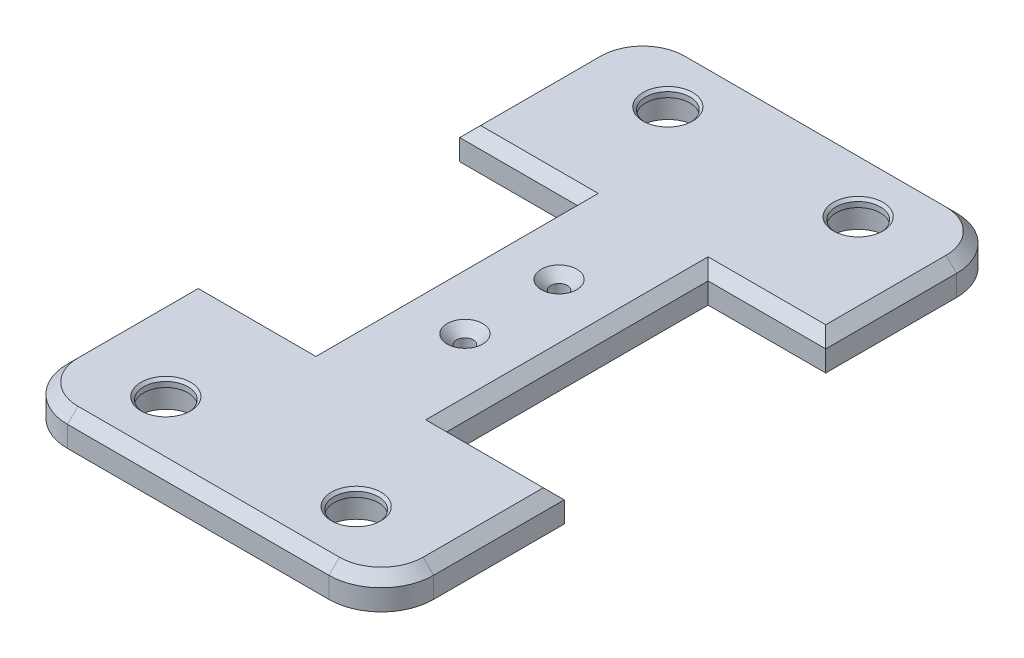
SolidWorks part; units mm, degrees
ref_plane "Plan de face" through (0, 0, 0) normal (0, 0, 1) x (1, 0, 0)
ref_plane "Plan de dessus" through (0, 0, 0) normal (0, 1, 0) x (1, 0, 0)
ref_plane "Plan de droite" through (0, 0, 0) normal (1, 0, 0) x (0, 0, -1)
sketch "Esquisse2" plane through (0, 0, 0) normal (0, 1, 0) x (1, 0, 0)
  line L0 (0, -60) -> (0, 60) construction
  line L1 (0, 0) -> (-68.0838, 0) construction
  line L2 (-12.5, -25) -> (-12.5, 25)
  line L3 (-12.5, 25) -> (-35, 25)
  line L4 (-35, 25) -> (-35, 60)
  line L5 (-35, 60) -> (35, 60)
  line L6 (12.5, -25) -> (12.5, 25)
  line L7 (35, 25) -> (35, 60)
  line L8 (12.5, 25) -> (35, 25)
  line L9 (12.5, -25) -> (35, -25)
  line L10 (35, -25) -> (35, -60)
  line L11 (-35, -60) -> (35, -60)
  line L12 (-35, -25) -> (-35, -60)
  line L13 (-12.5, -25) -> (-35, -25)
  circle A0 centre (-18.2, 48) radius 4.25
  circle A1 centre (18.2, 48) radius 4.25
  circle A2 centre (18.2, -48) radius 4.25
  circle A3 centre (-18.2, -48) radius 4.25
  circle A4 centre (0, 9) radius 1.6
  circle A5 centre (0, -9) radius 1.6
  point P24 (12.5, 0)
  point P27 (-12.5, 0)
  dimension "D5" = 8.5
  dimension "D8" = 3.2
  dimension "D9" = 3.2
  dimension "D10" = 9
  dimension "D11" = 9
  dimension "D1" = 60
  dimension "D2" = 35
  dimension "D3" = 35
  dimension "D4" = 12.5
  dimension "D6" = 16.8
  dimension "D7" = 12
extrude "Boss.-Extru.1" add sketch "Esquisse2" along normal blind 6
fillet "Congé1" radius 10 4 edges at (-35, 3, 60) (35, 3, 60) (35, 3, -60) (-35, 3, -60)
sketch "Esquisse3" plane through (0, 0, 0) normal (0, -1, 0) x (1, 0, 0)
  line L0 (0, 60) -> (0, -60) construction
  line L1 (-25, 60) -> (25, 60) construction
  line L2 (25, -60) -> (-25, -60) construction
  line L3 (-12.5, 0) -> (12.5, 0) construction
  line L4 (-12.5, -25) -> (-12.5, 25) construction
  line L5 (12.5, 25) -> (12.5, -25) construction
  circle A1 centre (-18.2, 48) radius 5.5
  circle A3 centre (18.2, 48) radius 5.5
  circle A4 centre (18.2, -48) radius 5.5
  circle A6 centre (-18.2, -48) radius 5.5
  dimension "D2" = 11
chamfer "Chanfrein1" distance 1.8 angle 45 2 edges at (0, 6, -7.4) (0, 6, 10.6)
chamfer "Chanfrein2" distance 2 angle 45 16 edges at (-23.75, 6, 25) (-12.5, 6, 0) (-23.75, 6, -25) (35, 6, -37.5) (-35, 6, -37.5) (32.0711, 6, -57.0711) (-32.0711, 6, -57.0711) (0, 6, -60) (-35, 6, 37.5) (-32.0711, 6, 57.0711) (0, 6, 60) (32.0711, 6, 57.0711) (23.75, 6, -25) (12.5, 6, 0) (23.75, 6, 25) (35, 6, 37.5)
extrude "Enlèv. mat.-Extru.1" cut sketch "Esquisse3" against normal blind 4.5
chamfer "Chanfrein3" distance 0.5 angle 45 4 edges at (-18.2, 6, -43.75) (18.2, 6, -52.25) (18.2, 6, 52.25) (-18.2, 6, 43.75)
